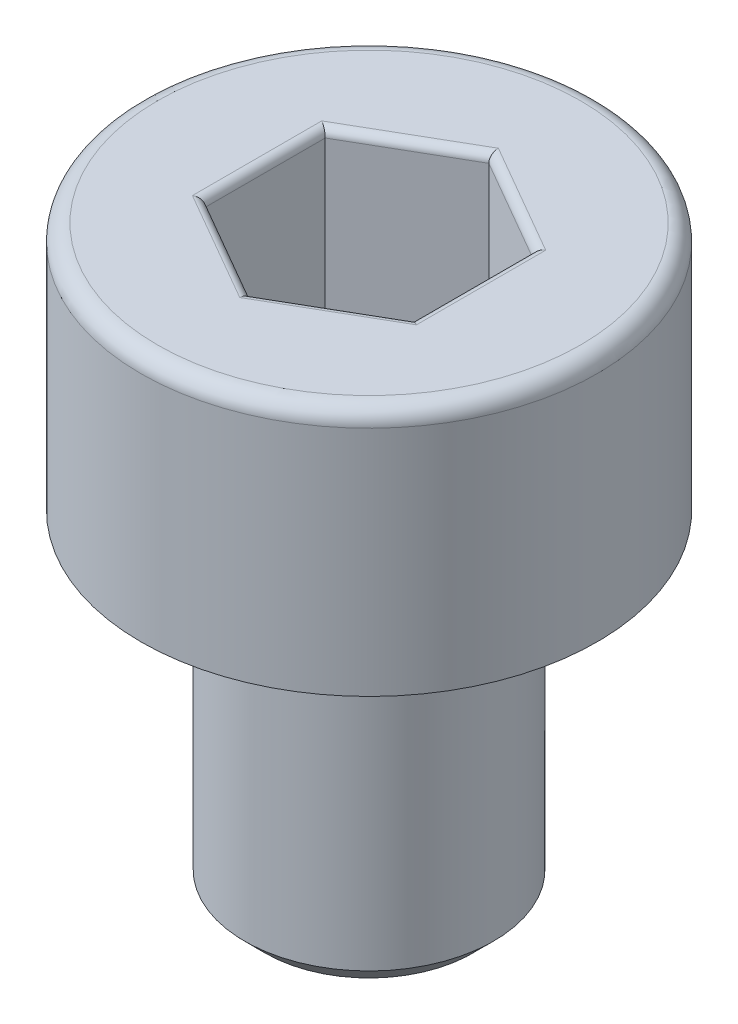
SolidWorks part; units mm, degrees
ref_plane "Front Plane" through (0, 0, 0) normal (0, 0, 1) x (1, 0, 0)
ref_plane "Top Plane" through (0, 0, 0) normal (0, 1, 0) x (1, 0, 0)
ref_plane "Right Plane" through (0, 0, 0) normal (1, 0, 0) x (0, 0, -1)
sketch "Sketch1" plane through (0, 0, 0) normal (0, 0, 1) x (1, 0, 0)
  line L0 (0, 0) -> (0, -47.0967) construction
  line L1 (0, -7) -> (-1.5, -7)
  line L2 (-1.5, -7) -> (-1.5, -3)
  line L3 (-1.5, -3) -> (-2.75, -3)
  line L4 (-2.75, -3) -> (-2.75, 0)
  line L5 (-2.75, 0) -> (0, 0)
  line L6 (0, 0) -> (0, -7)
  dimension "D1" = 4
  dimension "d" = 3
  dimension "k" = 3
  dimension "dk" = 5.5
revolve "Revolve1" add sketch "Sketch1" angle 360 about L0
chamfer "Chamfer1" distance 0.25 angle 45 2 edges at (0, -3, 1.5) (0, -7, 1.5)
fillet "Fillet1" radius 0.2 1 edges at (0, 0, 2.75)
sketch "Sketch2" plane through (0, 0, 0) normal (0, 1, 0) x (1, 0, 0)
  line L1 (0, 1.4434) -> (-1.25, 0.7217)
  line L2 (-1.25, 0.7217) -> (-1.25, -0.7217)
  line L3 (-1.25, -0.7217) -> (0, -1.4434)
  line L4 (0, -1.4434) -> (1.25, -0.7217)
  line L5 (1.25, -0.7217) -> (1.25, 0.7217)
  line L6 (1.25, 0.7217) -> (0, 1.4434)
  circle A0 centre (0, 0) radius 1.25 construction
  dimension "s" = 2.5
extrude "Cut-Extrude1" cut sketch "Sketch2" against normal blind 2
fillet "Fillet2" radius 0.1 12 edges at (-0.625, 0, -1.0825) (-1.25, 0, 0) (-0.625, 0, 1.0825) (0.625, 0, 1.0825) (1.25, 0, 0) (0.625, 0, -1.0825) (1.25, -2, 0) (0.625, -2, 1.0825) (-0.625, -2, 1.0825) (-1.25, -2, 0) (-0.625, -2, -1.0825) (0.625, -2, -1.0825)
